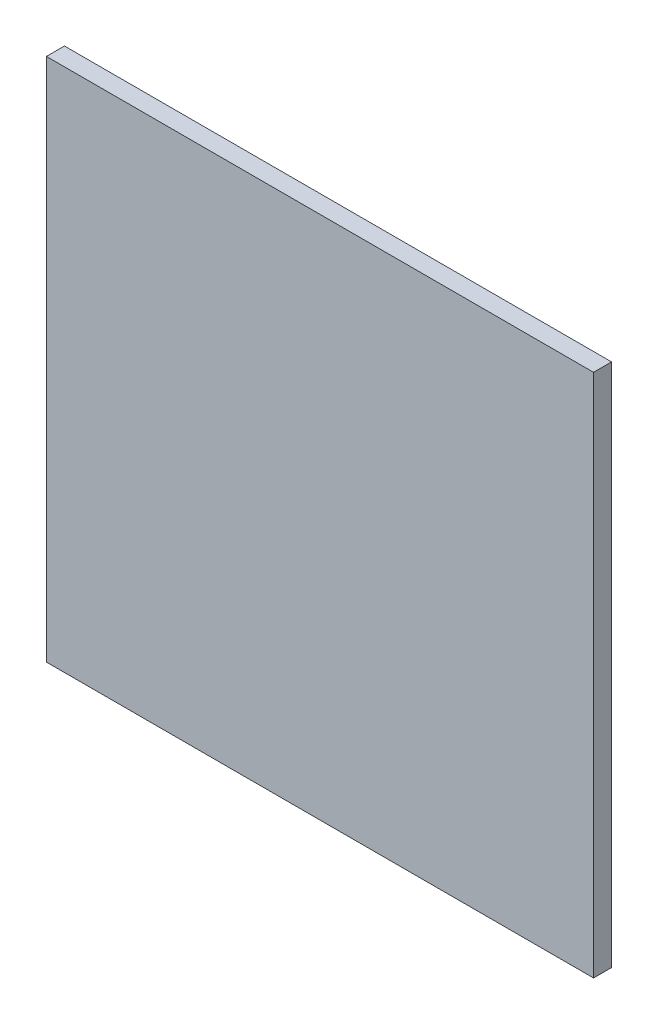
SolidWorks part; units mm, degrees
ref_plane "Front Plane" through (0, 0, 0) normal (0, 0, 1) x (1, 0, 0)
ref_plane "Top Plane" through (0, 0, 0) normal (0, 1, 0) x (1, 0, 0)
ref_plane "Right Plane" through (0, 0, 0) normal (1, 0, 0) x (0, 0, -1)
sketch "Sketch2" plane through (0, 0, 0) normal (0, 0, 1) x (1, 0, 0)
  line L0 (75.184, 76.2) -> (5.464, 76.2) construction
  line L1 (-2.1835, 79.2) -> (82.8165, 79.2)
  line L2 (-2.1835, 79.2) -> (-2.1835, -2.0443)
  line L3 (-2.1835, -2.0443) -> (82.8165, -2.0443)
  line L4 (82.8165, 79.2) -> (82.8165, -2.0443)
  dimension "D1" = 3
  dimension "D2" = 85
sketch "Sketch3" plane through (0, 0, 0) normal (0, 0, 1) x (1, 0, 0)
  line L0 (-2.1835, 79.2) -> (82.8165, 79.2) construction
  line L1 (-5.1835, 82.2) -> (85.8165, 82.2)
  line L2 (-5.1835, 82.2) -> (-5.1835, -5.0443)
  line L3 (-5.1835, -5.0443) -> (85.8165, -5.0443)
  line L4 (85.8165, 82.2) -> (85.8165, -5.0443)
  line L5 (-2.1835, -2.0443) -> (82.8165, -2.0443) construction
  line L6 (82.8165, 79.2) -> (82.8165, -2.0443) construction
  line L7 (-2.1835, 79.2) -> (-2.1835, -2.0443) construction
  dimension "D1" = 3
  dimension "D2" = 3
  dimension "D3" = 3
  dimension "D4" = 3
extrude "Boss-Extrude1" add sketch "Sketch3" along normal blind 2 and the other way blind 1
sketch "Sketch5" plane through (0, -5.0443, 0) normal (0, -1, 0) x (1, 0, 0)
  line L0 (41.964, 30.5585) -> (24.964, 30.5585) construction
  line L1 (24.464, 16.1885) -> (42.464, 16.1885)
  line L2 (24.464, 16.1885) -> (24.464, 31.0585)
  line L3 (24.464, 31.0585) -> (42.464, 31.0585)
  line L4 (42.464, 16.1885) -> (42.464, 31.0585)
  line L5 (24.464, 16.1885) -> (42.464, 31.0585) construction
  line L6 (24.464, 31.0585) -> (42.464, 16.1885) construction
  line L7 (41.964, 16.6885) -> (24.964, 16.6885) construction
  line L8 (41.964, 16.6885) -> (41.964, 30.5585) construction
  line L9 (24.964, 16.6885) -> (24.964, 30.5585) construction
  circle A0 centre (72.1076, 23.6235) radius 7
  point P0 (33.464, 23.6235)
  dimension "D1" = 0.5
  dimension "D2" = 0.5
  dimension "D3" = 0.5
  dimension "D4" = 0.5
